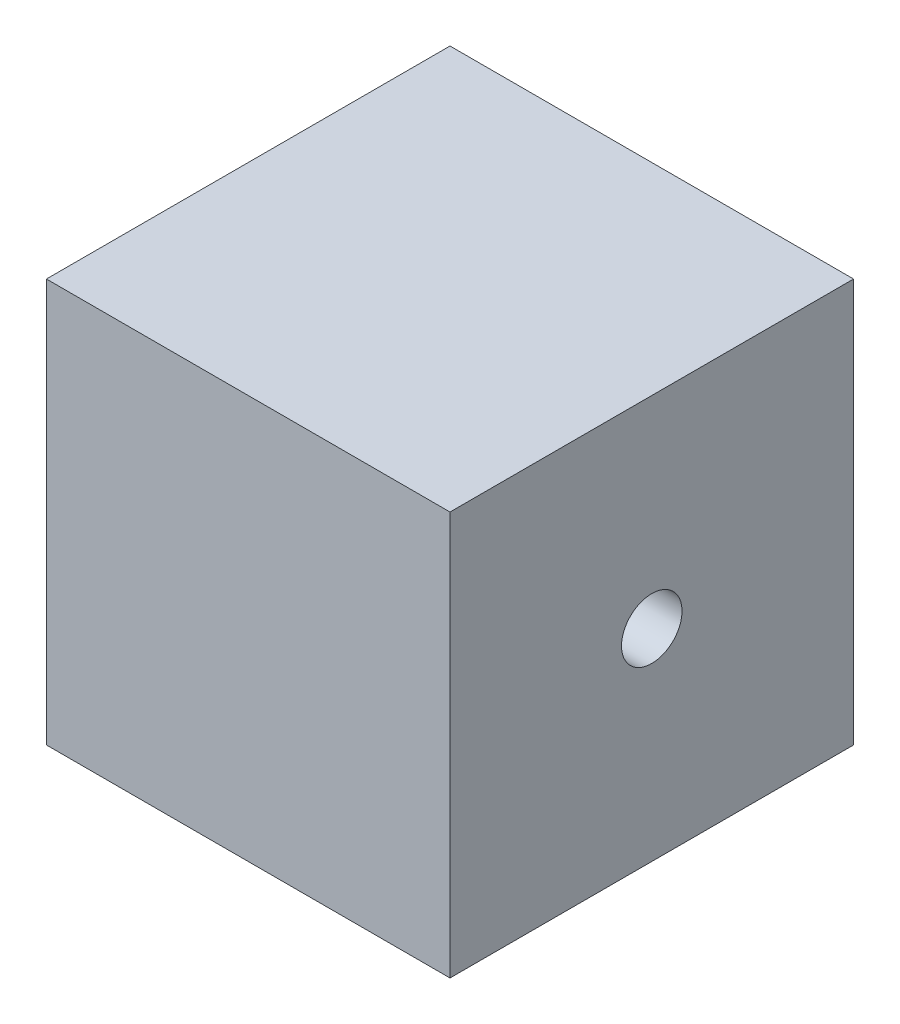
SolidWorks part; units mm, degrees
ref_plane "Front Plane" through (0, 0, 0) normal (0, 0, 1) x (1, 0, 0)
ref_plane "Top Plane" through (0, 0, 0) normal (0, 1, 0) x (1, 0, 0)
ref_plane "Right Plane" through (0, 0, 0) normal (1, 0, 0) x (0, 0, -1)
sketch "Sketch1" plane through (0, 0, 0) normal (0, 1, 0) x (1, 0, 0)
  line L1 (10, -10) -> (-10, -10)
  line L2 (10, -10) -> (10, 10)
  line L3 (10, 10) -> (-10, 10)
  line L4 (-10, -10) -> (-10, 10)
  line L5 (10, -10) -> (-10, 10) construction
  line L6 (10, 10) -> (-10, -10) construction
  point P0 (0, 0)
extrude "Boss-Extrude1" add sketch "Sketch1" along normal blind 20
sketch "Sketch3" plane through (-10, 0, 0) normal (-1, 0, 0) x (0, 0, 1)
  circle A0 centre (0, 10) radius 1.5
extrude "Cut-Extrude1" cut sketch "Sketch3" against normal blind 20
